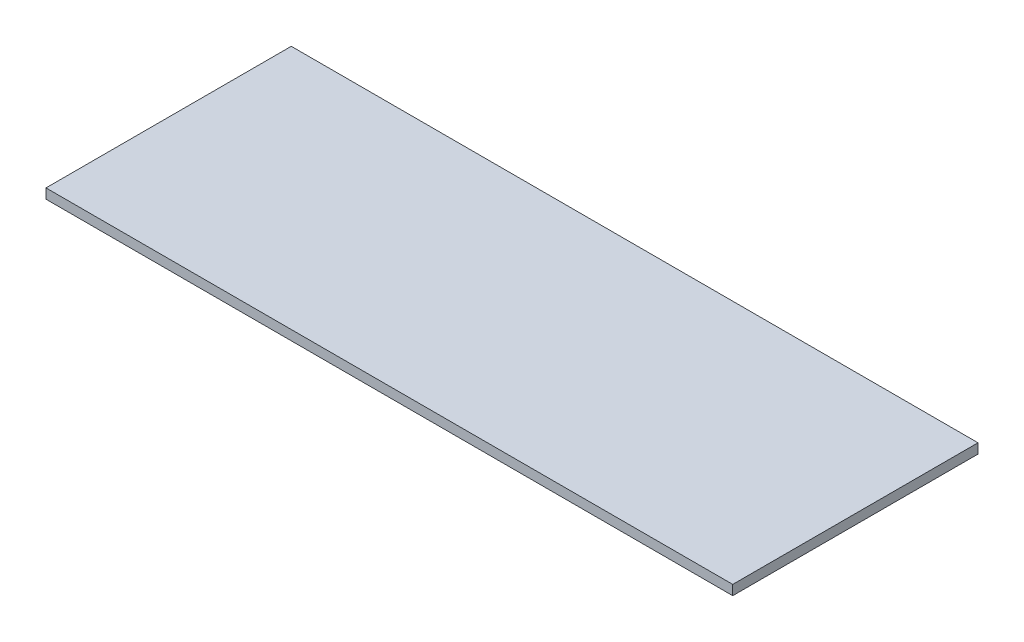
SolidWorks part; units mm, degrees
ref_plane "Front Plane" through (0, 0, 0) normal (0, 0, 1) x (1, 0, 0)
ref_plane "Top Plane" through (0, 0, 0) normal (0, 1, 0) x (1, 0, 0)
ref_plane "Right Plane" through (0, 0, 0) normal (1, 0, 0) x (0, 0, -1)
sketch "Sketch1" plane through (0, 0, 0) normal (0, 1, 0) x (1, 0, 0)
  line L1 (-24.4856, 8.0041) -> (45.5144, 8.0041)
  line L2 (-24.4856, 8.0041) -> (-24.4856, -16.9959)
  line L3 (-24.4856, -16.9959) -> (45.5144, -16.9959)
  line L4 (45.5144, 8.0041) -> (45.5144, -16.9959)
  line L5 (-24.4856, 8.0041) -> (45.5144, -16.9959) construction
  line L6 (-24.4856, -16.9959) -> (45.5144, 8.0041) construction
  point P4 (10.5144, -4.4959)
  dimension "D1" = 70
  dimension "D2" = 25
extrude "Boss-Extrude1" add sketch "Sketch1" along normal blind 1
